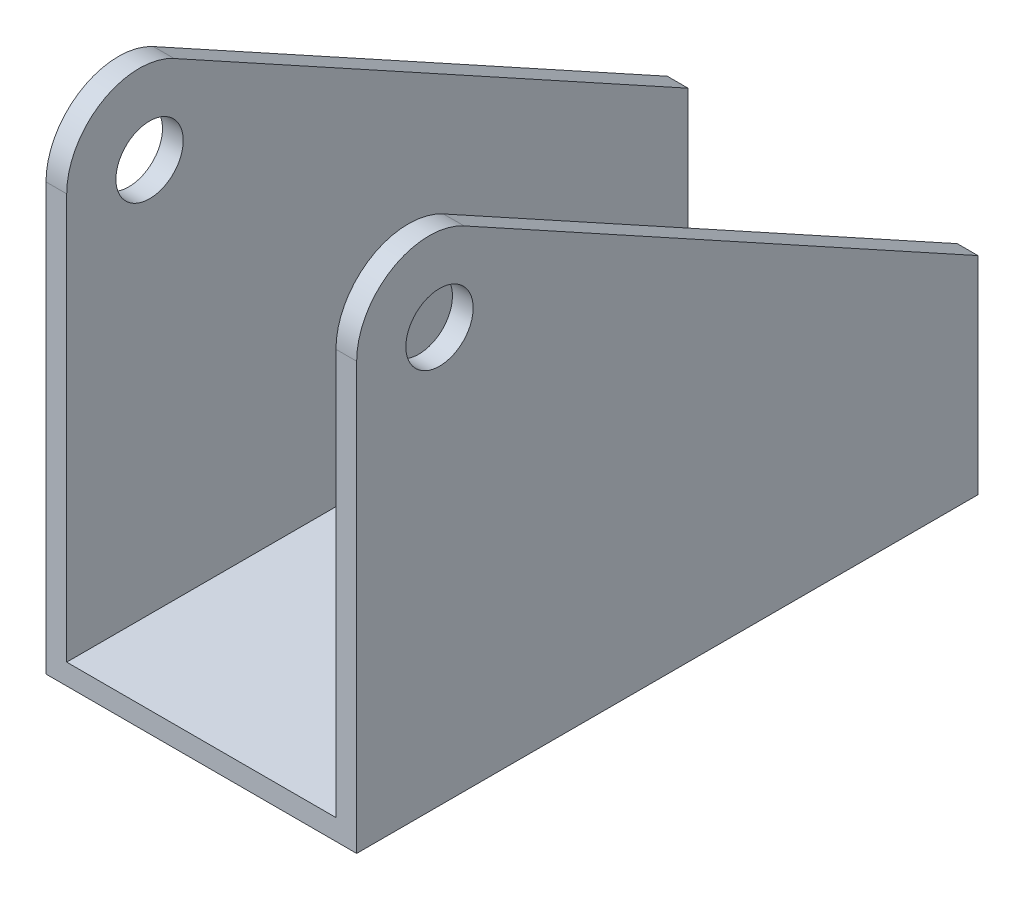
SolidWorks part; units mm, degrees
ref_plane "前视基准面" through (0, 0, 0) normal (0, 0, 1) x (1, 0, 0)
ref_plane "上视基准面" through (0, 0, 0) normal (0, 1, 0) x (1, 0, 0)
ref_plane "右视基准面" through (0, 0, 0) normal (1, 0, 0) x (0, 0, -1)
sketch "草图1" plane through (0, 0, 0) normal (0, 0, 1) x (1, 0, 0)
  line L0 (-25.3132, 0) -> (25.4167, 0) construction
  line L1 (0, 42.3624) -> (0, -24.8288) construction
  line L2 (-13, -20.7978) -> (-13, -73.7978)
  line L3 (-15, -20.7978) -> (-13, -20.7978)
  line L4 (-15, -20.7978) -> (-15, -75.7978)
  line L5 (-15, -75.7978) -> (15, -75.7978)
  line L6 (15, -20.7978) -> (15, -75.7978)
  line L7 (-13, -73.7978) -> (13, -73.7978)
  line L8 (13, -73.7978) -> (13, -20.7978)
  line L9 (13, -20.7978) -> (15, -20.7978)
  dimension "D1" = 2
  dimension "D2" = 2
  dimension "D3" = 55
  dimension "D4" = 30
extrude "凸台-拉伸1" add sketch "草图1" along normal blind 60
sketch "草图2" plane through (15, 0, 0) normal (1, 0, 0) x (0, 0, -1)
  line L0 (-60, -20.7978) -> (-60, -22.7978)
  line L1 (-60, -75.7978) -> (-60, -20.7978) construction
  line L2 (-60, -22.7978) -> (0, -55.7978)
  line L3 (0, -75.7978) -> (0, -20.7978) construction
  line L4 (0, -55.7978) -> (0, -20.7978)
  line L5 (0, -20.7978) -> (-60, -20.7978)
  line L6 (-60, -75.7978) -> (0, -75.7978) construction
  line L7 (-52.5204, -35.7978) -> (-24.1962, -35.7978) construction
  line L8 (-52, -38.7706) -> (-52, -78.2038) construction
  circle A0 centre (-52, -35.7978) radius 3.25
  dimension "D5" = 6.5
  dimension "D1" = 53
  dimension "D2" = 20
  dimension "D3" = 8
  dimension "D4" = 40
extrude "切除-拉伸1" cut sketch "草图2" against normal through all
fillet "圆角1" radius 7 2 edges at (14, -22.7978, 60) (-14, -22.7978, 60)
sketch "草图3" plane through (0, -73.7978, 0) normal (0, 1, 0) x (1, 0, 0)
  line L0 (-23.7429, -12) -> (24.7461, -12) construction
  line L1 (0, 24.9959) -> (0, -63.4851) construction
  line L2 (13, 0) -> (-13, 0) construction
  circle A0 centre (0, -12) radius 3.25
  dimension "D1" = 6.5
  dimension "D2" = 12
extrude "切除-拉伸2" cut sketch "草图3" against normal through all
